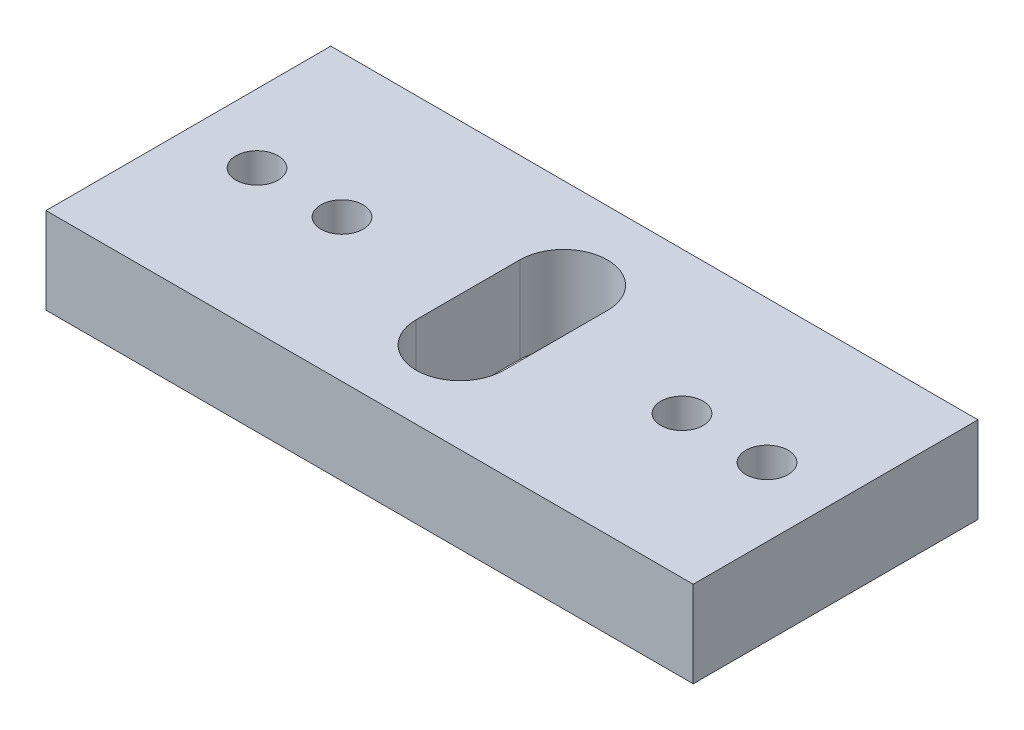
SolidWorks part; units mm, degrees
ref_plane "Front Plane" through (0, 0, 0) normal (0, 0, 1) x (1, 0, 0)
ref_plane "Top Plane" through (0, 0, 0) normal (0, 1, 0) x (1, 0, 0)
ref_plane "Right Plane" through (0, 0, 0) normal (1, 0, 0) x (0, 0, -1)
sketch "Sketch1" plane through (0, 0, 0) normal (0, 1, 0) x (1, 0, 0)
  line L0 (0, 0) -> (0, 10.1312) construction
  line L1 (0, 0) -> (-39.2364, 0) construction
  line L2 (19.05, 8.382) -> (-19.05, 8.382)
  line L3 (-19.05, 8.382) -> (-19.05, -8.382)
  line L4 (0, 0) -> (0, -10.5582) construction
  line L5 (19.05, 8.382) -> (19.05, -8.382)
  line L6 (19.05, -8.382) -> (-19.05, -8.382)
  line L9 (2.5686, -3.048) -> (2.5686, 3.048)
  line L11 (-2.5908, -3.048) -> (-2.5908, 3.048)
  arc A0 (2.5686, 3.048) -> (-2.5908, 3.048) centre (-0.0111, 3.048) ccw
  circle A1 centre (-10.0076, 0) radius 1.2446
  circle A2 centre (-15.0114, 0) radius 1.2446
  arc A3 (2.5686, -3.048) -> (-2.5908, -3.048) centre (-0.0111, -3.048) cw
  circle A13 centre (15.0114, 0) radius 1.2446
  circle A14 centre (10.0076, 0) radius 1.2446
  point P14 (0, 8.382)
  point P16 (-19.05, 0)
  point P17 (19.05, 0)
  point P20 (2.5686, 0)
  point P24 (-2.5908, 0)
  dimension "D1" = 3.048
  dimension "D2" = 2.4892
  dimension "D5" = 2.4892
  dimension "D7" = 8.382
  dimension "D10" = 2.5908
  dimension "D11" = 2.5797
  dimension "D3" = 10.0076
  dimension "D4" = 5.0038
  dimension "D6" = 19.05
  dimension "D8" = 5.1594
  dimension "D9" = 6.096
extrude "Boss-Extrude1" add sketch "Sketch1" along normal blind 5.08
